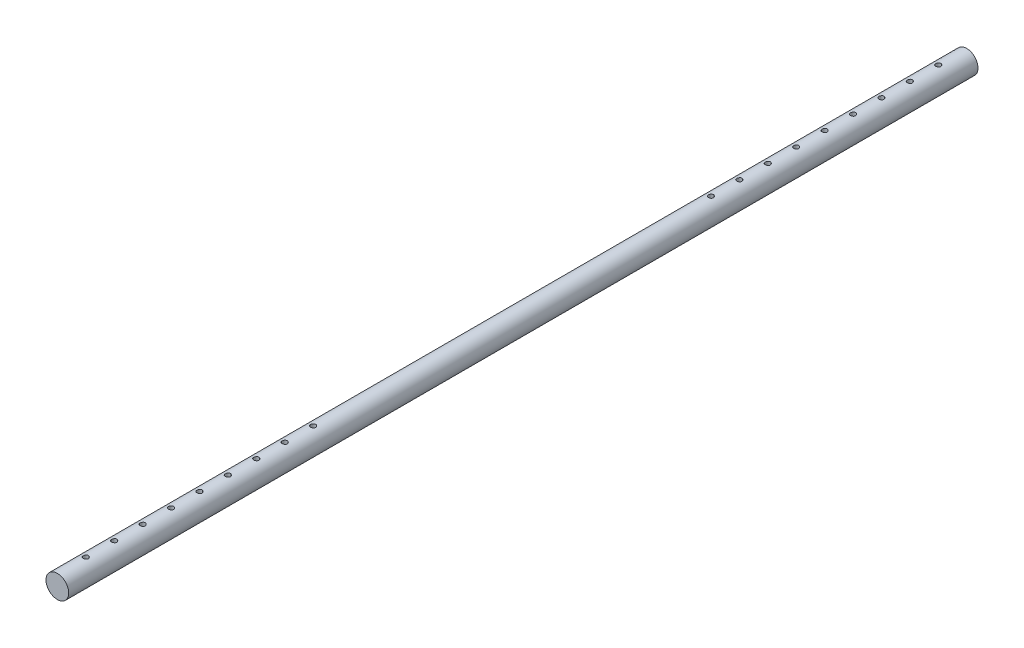
SolidWorks part; units mm, degrees
ref_plane "Front Plane" through (0, 0, 0) normal (0, 0, 1) x (1, 0, 0)
ref_plane "Top Plane" through (0, 0, 0) normal (0, 1, 0) x (1, 0, 0)
ref_plane "Right Plane" through (0, 0, 0) normal (1, 0, 0) x (0, 0, -1)
sketch "Sketch1" plane through (0, 0, 0) normal (0, 0, 1) x (1, 0, 0)
  circle A0 centre (0, 0) radius 10
  dimension "D1" = 20
extrude "Boss-Extrude1" add sketch "Sketch1" along normal blind 800
sketch "Sketch2" plane through (0, 0, 0) normal (0, 1, 0) x (1, 0, 0)
  line L0 (0, 0) -> (0, -25) construction
  line L1 (0, -25) -> (0, -50) construction
  line L2 (0, -50) -> (0, -75) construction
  line L3 (0, -75) -> (0, -725) construction
  line L4 (0, -725) -> (0, -750) construction
  line L5 (0, -750) -> (0, -775) construction
  line L6 (0, -775) -> (0, -800) construction
  line L7 (-10, -800) -> (10, -800) construction
  circle A0 centre (0, -25) radius 2.25
  circle A1 centre (0, -775) radius 2.25
  circle A2 centre (0, -750) radius 2.25
  circle A3 centre (0, -725) radius 2.25
  circle A4 centre (0, -50) radius 2.25
  circle A6 centre (0, -75) radius 2.25
  circle A7 centre (0, -100) radius 2.25
  circle A8 centre (0, -125) radius 2.25
  circle A9 centre (0, -150) radius 2.25
  circle A10 centre (0, -175) radius 2.25
  circle A11 centre (0, -200) radius 2.25
  circle A12 centre (0, -225) radius 2.25
  circle A13 centre (0, -700) radius 2.25
  circle A14 centre (0, -675) radius 2.25
  circle A15 centre (0, -650) radius 2.25
  circle A16 centre (0, -625) radius 2.25
  circle A17 centre (0, -600) radius 2.25
  circle A18 centre (0, -575) radius 2.25
  dimension "D1" = 4.5
  dimension "D2" = 25
  dimension "D3" = 8
  dimension "D4" = 7
extrude "Cut-Extrude1" cut sketch "Sketch2" against normal up to next and the other way up to next
